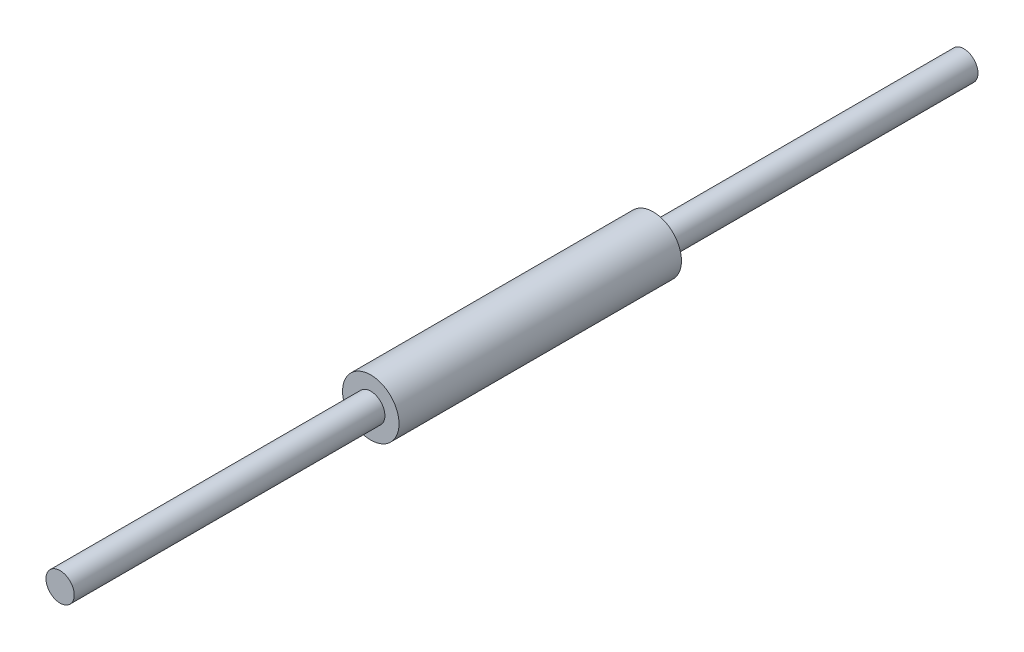
SolidWorks part; units mm, degrees
material "1023 Carbon Steel Sheet (SS)"
ref_plane "Front Plane" through (0, 0, 0) normal (0, 0, 1) x (1, 0, 0)
ref_plane "Top Plane" through (0, 0, 0) normal (0, 1, 0) x (1, 0, 0)
ref_plane "Right Plane" through (0, 0, 0) normal (1, 0, 0) x (0, 0, -1)
sketch "Sketch2" plane through (0, 0, 0) normal (0, 0, 1) x (1, 0, 0)
  circle A0 centre (0, 0) radius 25
  dimension "D1" = 50
extrude "Boss-Extrude1" add sketch "Sketch2" along normal mid plane 250
sketch "Sketch4" plane through (0, 0, 0) normal (0, 0, 1) x (1, 0, 0)
  circle A0 centre (0, 0) radius 12.5
  dimension "D1" = 25
extrude "Boss-Extrude2" add sketch "Sketch4" along normal mid plane 800
